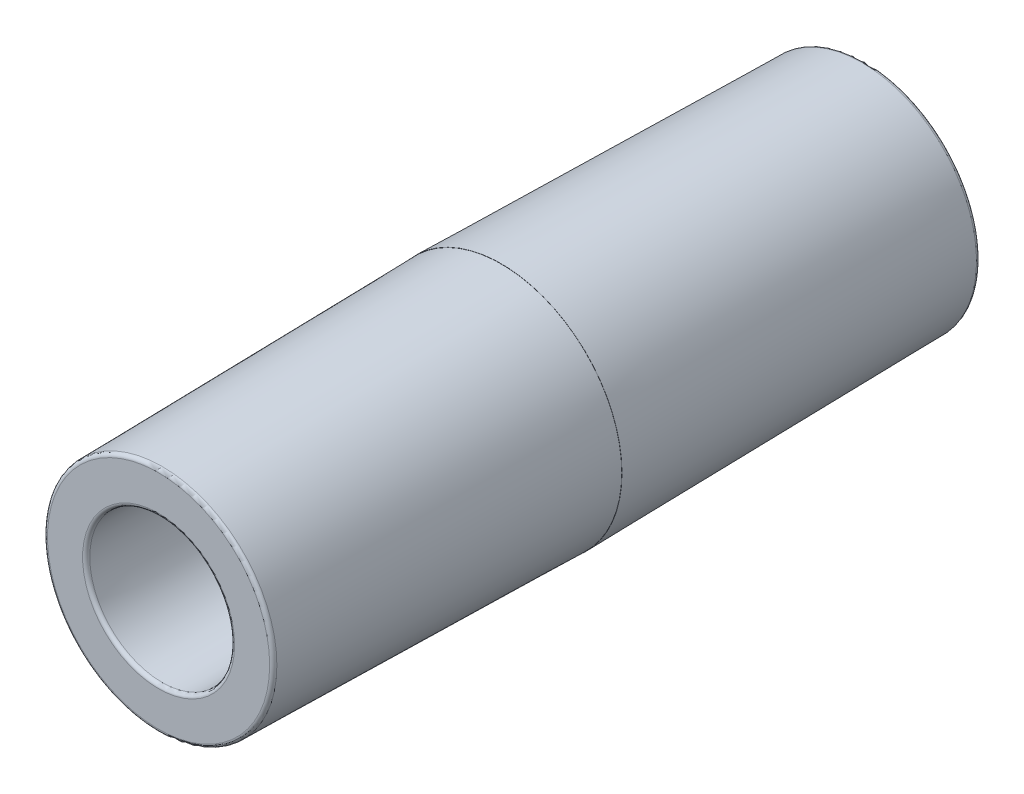
SolidWorks part; units mm, degrees
material "ABS"
ref_plane "Front Plane" through (0, 0, 0) normal (0, 0, 1) x (1, 0, 0)
ref_plane "Top Plane" through (0, 0, 0) normal (0, 1, 0) x (1, 0, 0)
ref_plane "Right Plane" through (0, 0, 0) normal (1, 0, 0) x (0, 0, -1)
ref_plane "Plane1" through (0, 0, 0) normal (0, -1, 0) x (1, 0, 0)
sketch "Sketch1" plane through (0, 0, 0) normal (0, -1, 0) x (1, 0, 0)
  line L0 (5.0471, 23.876) -> (4.8387, 0)
  line L1 (4.8387, 0) -> (4.8514, 0)
  line L2 (4.8514, 0) -> (5.0731, -25.4)
  line L3 (5.0731, -25.4) -> (7.9767, -25.4)
  line L4 (7.9767, -25.4) -> (8.4201, 0)
  line L5 (8.4201, 0) -> (8.4074, 0)
  line L6 (8.4074, 0) -> (7.9906, 23.876)
  line L7 (7.9906, 23.876) -> (5.0471, 23.876)
  line L8 (0, 23.868) -> (0, -23.868) construction
  line L9 (0, 0) -> (11.7054, 0) construction
  dimension "D1" = 25.4
  dimension "D2" = 23.876
  dimension "D3" = 0.5
  dimension "D4" = 0.5
  dimension "D5" = 4.8387
  dimension "D6" = 0.0127
  dimension "D7" = 16.8402
  dimension "D8" = 91
  dimension "D9" = 91
  dimension "D10" = 0.0127
revolve "Revolve1" add sketch "Sketch1" angle 360 about L8
fillet "Fillet1" radius 0.254 4 edges at (-7.9906, 0, 23.876) (-5.0471, 0, 23.876) (-5.0731, 0, -25.4) (-7.9767, 0, -25.4)
